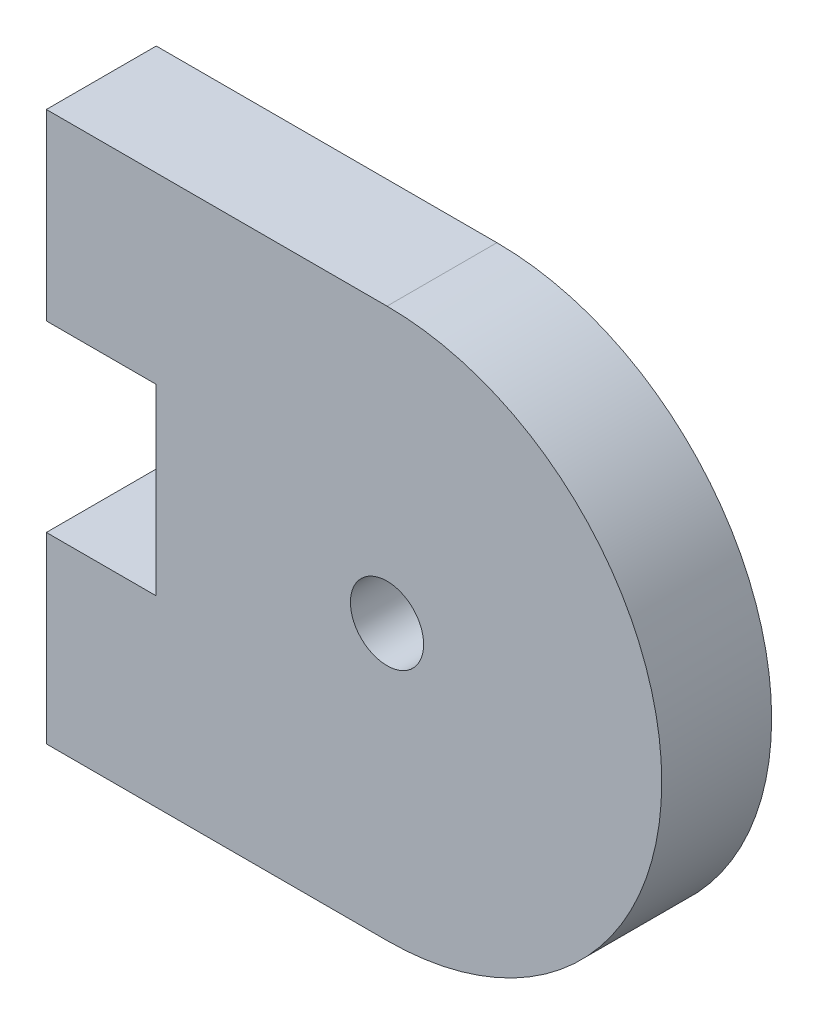
SolidWorks part; units mm, degrees
ref_plane "Alzado" through (0, 0, 0) normal (0, 0, 1) x (1, 0, 0)
ref_plane "Planta" through (0, 0, 0) normal (0, 1, 0) x (1, 0, 0)
ref_plane "Vista lateral" through (0, 0, 0) normal (1, 0, 0) x (0, 0, -1)
sketch "Model" plane through (0, 0, 0) normal (0, 0, 1) x (1, 0, 0)
  line L0 (26.66, 16.3669) -> (26.66, 11.3669)
  line L1 (35.96, 26.3669) -> (26.66, 26.3669)
  line L2 (26.66, 11.3669) -> (35.96, 11.3669)
  line L3 (29.66, 16.3669) -> (26.66, 16.3669)
  line L4 (29.66, 21.3669) -> (29.66, 16.3669)
  line L5 (26.66, 21.3669) -> (29.66, 21.3669)
  line L6 (26.66, 21.3669) -> (26.66, 26.3669)
  circle A0 centre (35.96, 18.8669) radius 1
  arc A2 (35.96, 11.3669) -> (35.96, 26.3669) centre (35.96, 18.8669) ccw
sketch "Croquis2" plane through (0, 0, 0) normal (0, 0, 1) x (1, 0, 0)
  circle A0 centre (35.96, 18.8669) radius 2.15
extrude "Saliente-Extruir1" add sketch "Model" along normal blind 3
extrude "Cortar-Extruir1" cut sketch "Croquis2" along normal blind 1
